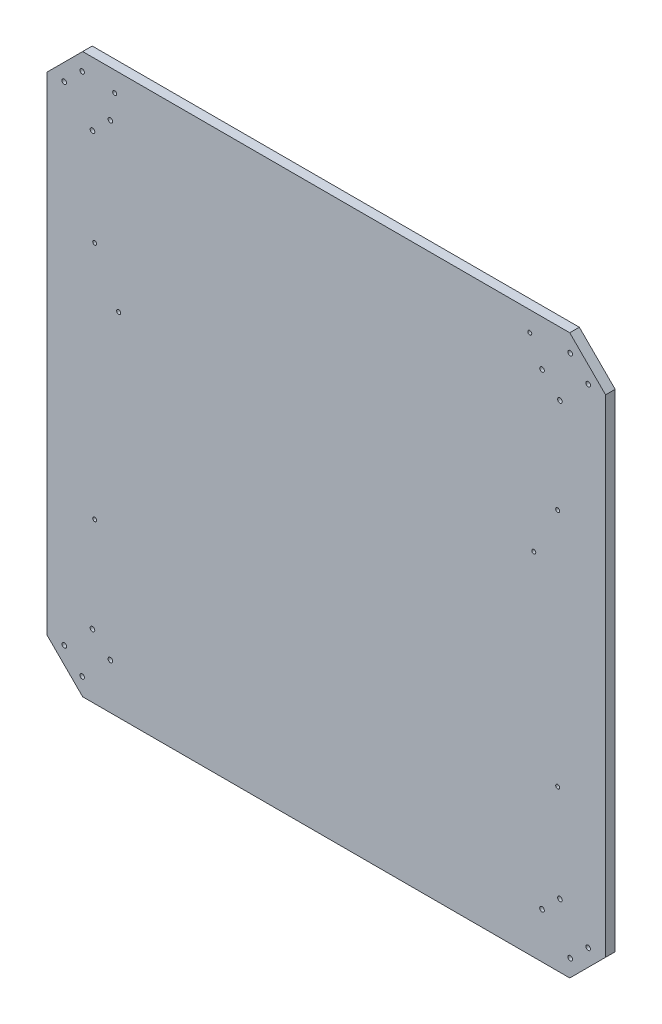
SolidWorks part; units mm, degrees
material "6061 Alloy"
ref_plane "Front Plane" through (0, 0, 0) normal (0, 0, 1) x (1, 0, 0)
ref_plane "Top Plane" through (0, 0, 0) normal (0, 1, 0) x (1, 0, 0)
ref_plane "Right Plane" through (0, 0, 0) normal (1, 0, 0) x (0, 0, -1)
sketch "Sketch1" plane through (0, 0, 0) normal (0, 0, 1) x (1, 0, 0)
  line L1 (-350, -350) -> (350, -350)
  line L2 (-350, -350) -> (-350, 350)
  line L3 (-350, 350) -> (350, 350)
  line L4 (350, -350) -> (350, 350)
  line L5 (-350, -350) -> (350, 350) construction
  line L6 (-350, 350) -> (350, -350) construction
  point P0 (0, 0)
  dimension "D1" = 700
  dimension "D2" = 700
extrude "Boss-Extrude1" add sketch "Sketch1" along normal blind 12
sketch "Sketch3" plane through (0, 0, 12) normal (0, 0, 1) x (1, 0, 0)
  line L0 (350, 350) -> (-350, -350) construction
  line L1 (350, -350) -> (-350, 350) construction
  line L2 (0, 202.0632) -> (0, -117.5673) construction
  line L3 (305.0987, 350) -> (350, 305.0987) construction
  line L4 (-113.0304, 0) -> (122.2862, 0) construction
  line L5 (350, 350) -> (-350, 350) construction
  line L6 (350, -350) -> (350, 350) construction
  line L7 (305.0987, 350) -> (248.5302, 293.4315) construction
  line L8 (350, 305.0987) -> (293.4315, 248.5302) construction
  line L9 (248.5302, 293.4315) -> (293.4315, 248.5302) construction
  line L10 (-350, 305.0987) -> (-293.4315, 248.5302) construction
  line L11 (-248.5302, 293.4315) -> (-293.4315, 248.5302) construction
  line L12 (-305.0987, 350) -> (-248.5302, 293.4315) construction
  line L13 (-305.0987, 350) -> (-350, 305.0987) construction
  line L14 (305.0987, -350) -> (350, -305.0987) construction
  line L15 (305.0987, -350) -> (248.5302, -293.4315) construction
  line L16 (248.5302, -293.4315) -> (293.4315, -248.5302) construction
  line L17 (350, -305.0987) -> (293.4315, -248.5302) construction
  line L18 (-305.0987, -350) -> (-350, -305.0987) construction
  line L19 (-305.0987, -350) -> (-248.5302, -293.4315) construction
  line L20 (-248.5302, -293.4315) -> (-293.4315, -248.5302) construction
  line L21 (-350, -305.0987) -> (-293.4315, -248.5302) construction
  line L22 (327.5494, 327.5494) -> (270.9808, 270.9808) construction
  line L23 (276.8144, 321.7157) -> (321.7157, 276.8144) construction
  line L24 (350, 350) -> (305.0987, 350)
  line L25 (305.0987, 350) -> (350, 305.0987)
  line L26 (350, 305.0987) -> (350, 350)
  line L27 (-305.0987, 350) -> (-350, 305.0987)
  line L28 (-350, 350) -> (-305.0987, 350)
  line L29 (-350, 305.0987) -> (-350, 350)
  line L30 (305.0987, -350) -> (350, -305.0987)
  line L31 (350, -350) -> (305.0987, -350)
  line L32 (350, -305.0987) -> (350, -350)
  line L33 (-350, -350) -> (-305.0987, -350)
  line L34 (-350, -305.0987) -> (-350, -350)
  line L35 (-305.0987, -350) -> (-350, -305.0987)
  circle A0 centre (305.7174, 328.1681) radius 2.8916
  circle A1 centre (328.1681, 305.7174) radius 2.8916
  circle A2 centre (292.8127, 270.3621) radius 2.8916
  circle A3 centre (270.3621, 292.8127) radius 2.8916
  circle A4 centre (-270.3621, 292.8127) radius 2.8916
  circle A5 centre (-292.8127, 270.3621) radius 2.8916
  circle A6 centre (-305.7174, 328.1681) radius 2.8916
  circle A7 centre (-328.1681, 305.7174) radius 2.8916
  circle A8 centre (270.3621, -292.8127) radius 2.8916
  circle A9 centre (305.7174, -328.1681) radius 2.8916
  circle A10 centre (328.1681, -305.7174) radius 2.8916
  circle A11 centre (292.8127, -270.3621) radius 2.8916
  circle A12 centre (-270.3621, -292.8127) radius 2.8916
  circle A13 centre (-292.8127, -270.3621) radius 2.8916
  circle A14 centre (-305.7174, -328.1681) radius 2.8916
  circle A15 centre (-328.1681, -305.7174) radius 2.8916
  dimension "D1" = 63.5
  dimension "D2" = 80
  dimension "D3" = 31.75
  dimension "D4" = 50
extrude "Cut-Extrude2" cut sketch "Sketch3" against normal through all
sketch "Sketch4" plane through (0, 0, 12) normal (0, 0, 1) x (1, 0, 0)
  line L0 (0, 350) -> (0, -350) construction
  line L1 (305.0987, 350) -> (-305.0987, 350) construction
  line L2 (-305.0987, -350) -> (305.0987, -350) construction
  line L4 (350, -305.0987) -> (350, 305.0987) construction
  line L5 (350, 0) -> (-350, 0) construction
  line L6 (-350, 305.0987) -> (-350, -305.0987) construction
  line L8 (305.0987, 350) -> (-305.0987, 350) construction
  circle A0 centre (-290, 150) radius 2.5
  circle A1 centre (290, 150) radius 2.5
  circle A2 centre (290, -150) radius 2.5
  circle A3 centre (-290, -150) radius 2.5
  circle A6 centre (-265, 325) radius 2.5
  circle A7 centre (255, 325) radius 2.5
  circle A8 centre (-260, 90) radius 2.5
  circle A9 centre (260, 90) radius 2.5
  dimension "D1" = 5
  dimension "D4" = 5
  dimension "D2" = 580
  dimension "D3" = 300
  dimension "D5" = 260
  dimension "D6" = 520
  dimension "D7" = 520
extrude "Cut-Extrude3" cut sketch "Sketch4" against normal blind 20
